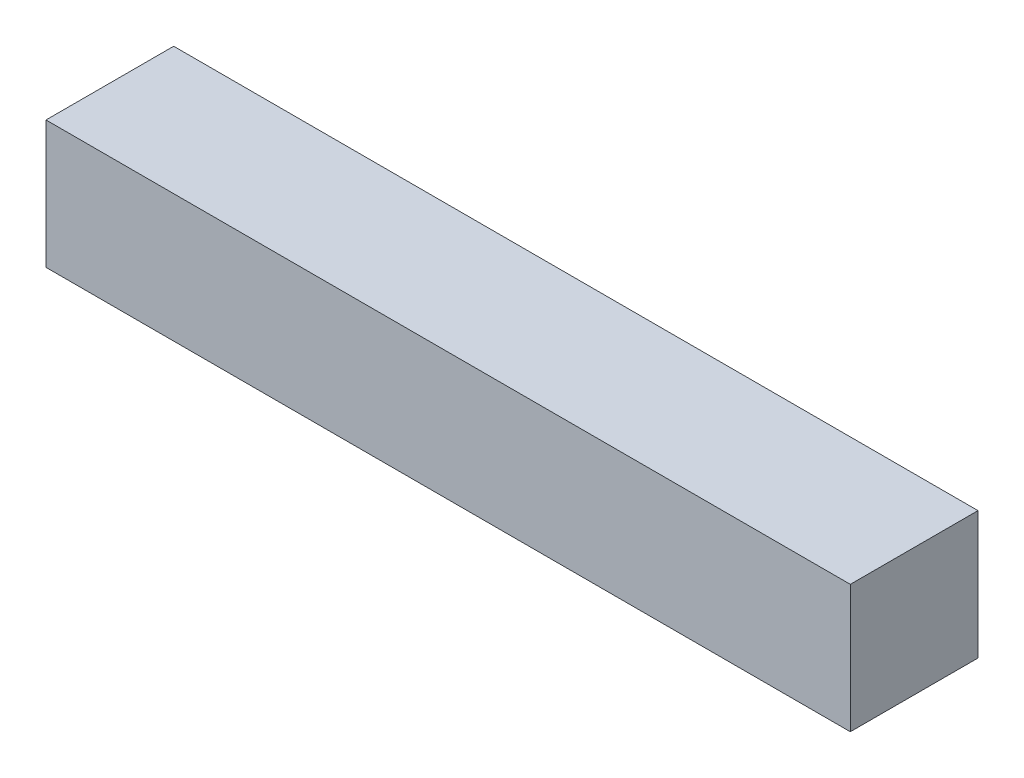
SolidWorks part; units mm, degrees
ref_plane "Front Plane" through (0, 0, 0) normal (0, 0, 1) x (1, 0, 0)
ref_plane "Top Plane" through (0, 0, 0) normal (0, 1, 0) x (1, 0, 0)
ref_plane "Right Plane" through (0, 0, 0) normal (1, 0, 0) x (0, 0, -1)
sketch "Sketch1" plane through (0, 0, 0) normal (0, 1, 0) x (1, 0, 0)
  line L0 (-40, 6.35) -> (40, -6.35) construction
  line L1 (-40, 6.35) -> (40, 6.35)
  line L2 (-40, 6.35) -> (-40, -6.35)
  line L3 (-40, -6.35) -> (40, -6.35)
  line L4 (40, 6.35) -> (40, -6.35)
  dimension "D1" = 80
  dimension "D2" = 12.7
extrude "Boss-Extrude1" add sketch "Sketch1" along normal blind 12.7
